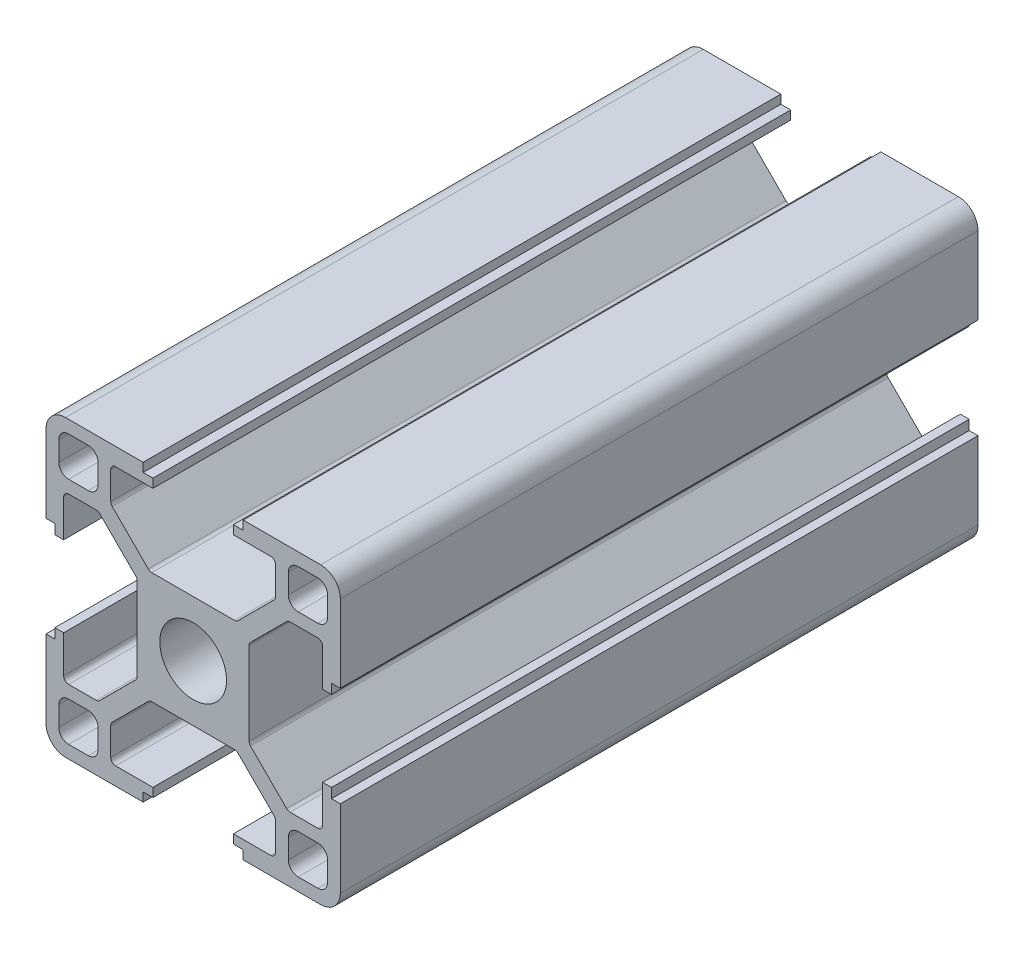
SolidWorks part; units mm, degrees
ref_plane "前视基准面" through (0, 0, 0) normal (0, 0, 1) x (1, 0, 0)
ref_plane "上视基准面" through (0, 0, 0) normal (0, 1, 0) x (1, 0, 0)
ref_plane "右视基准面" through (0, 0, 0) normal (1, 0, 0) x (0, 0, -1)
sketch "草图1" plane through (0, 0, 0) normal (0, 0, 1) x (1, 0, 0)
  line L0 (0, 0) -> (0, 65.3905) construction
  line L1 (0, 0) -> (64.2648, 0) construction
  line L2 (0, 0) -> (79.9729, 79.9729) construction
  line L3 (5.7, 0) -> (5.7, 4.4272)
  line L4 (5.7, 4.4272) -> (9.6728, 8.4)
  line L5 (9.6728, 8.4) -> (13.2, 8.4)
  line L6 (13.2, 8.4) -> (13.2, 4.1)
  line L7 (13.2, 4.1) -> (14.1, 4.1)
  line L8 (14.1, 4.1) -> (14.1, 5.1)
  line L9 (14.1, 5.1) -> (15, 5.1)
  line L10 (15, 5.1) -> (15, 15)
  line L11 (5.1, 15) -> (15, 15)
  line L12 (5.1, 14.1) -> (5.1, 15)
  line L13 (4.1, 14.1) -> (5.1, 14.1)
  line L14 (4.1, 13.2) -> (4.1, 14.1)
  line L15 (8.4, 13.2) -> (4.1, 13.2)
  line L16 (8.4, 9.6728) -> (8.4, 13.2)
  line L17 (4.4272, 5.7) -> (8.4, 9.6728)
  line L18 (0, 5.7) -> (4.4272, 5.7)
  line L20 (9.7, 9.7) -> (13.7, 9.7)
  line L21 (9.7, 9.7) -> (9.7, 13.7)
  line L22 (9.7, 13.7) -> (13.7, 13.7)
  line L23 (13.7, 9.7) -> (13.7, 13.7)
  line L24 (9.7, 9.7) -> (13.7, 13.7) construction
  line L25 (9.7, 13.7) -> (13.7, 9.7) construction
  line L26 (0, 5.7) -> (0, 0)
  line L27 (0, 0) -> (5.7, 0)
  point P9 (11.7, 11.7)
  dimension "D1" = 45
  dimension "D2" = 5.7
  dimension "D3" = 1.8
  dimension "D4" = 0.9
  dimension "D5" = 8.2
  dimension "D6" = 10.2
  dimension "D7" = 1.8
  dimension "D8" = 15
  dimension "D9" = 16.8
  dimension "D10" = 4
  dimension "D11" = 1.3
extrude "凸台-拉伸1" add sketch "草图1" along normal blind 65 contours L3 L4 L5 L6 L7 L8 L9 L10 L11 L12 L13 L14 L15 L16 L17 L18 L26 L27
fillet "圆角1" radius 1 4 edges at (9.7, 9.7, 32.5) (13.7, 9.7, 32.5) (9.7, 13.7, 32.5) (13.7, 13.7, 32.5)
fillet "圆角2" radius 2 1 edges at (15, 15, 32.5)
fillet "圆角3" radius 0.5 6 edges at (5.7, 4.4272, 32.5) (4.4272, 5.7, 32.5) (8.4, 13.2, 32.5) (8.4, 9.6728, 32.5) (9.6728, 8.4, 32.5) (13.2, 8.4, 32.5)
pattern_circular "阵列(圆周)1" count 4 over 360 about axis through (0, 0, 0) along (0, 0, 1) of "圆角2", "圆角3", "凸台-拉伸1", "圆角1"
sketch "草图2" plane through (0, 0, 65) normal (0, 0, 1) x (1, 0, 0)
  circle A0 centre (0, 0) radius 3.4
  dimension "D1" = 6.8
extrude "切除-拉伸1" cut sketch "草图2" against normal through all
sketch "草图3" plane through (-5.7, 0, 0) normal (-1, 0, 0) x (0, 0, 1)
  line L0 (-5.668, 0) -> (74.2169, 0) construction
  line L1 (0, -4.2201) -> (0, 4.2201) construction
  circle A0 centre (15, 0) radius 4.1
  dimension "D1" = 8.2
  dimension "D2" = 15
extrude "切除-拉伸2" cut sketch "草图3" against normal through all contours A0
